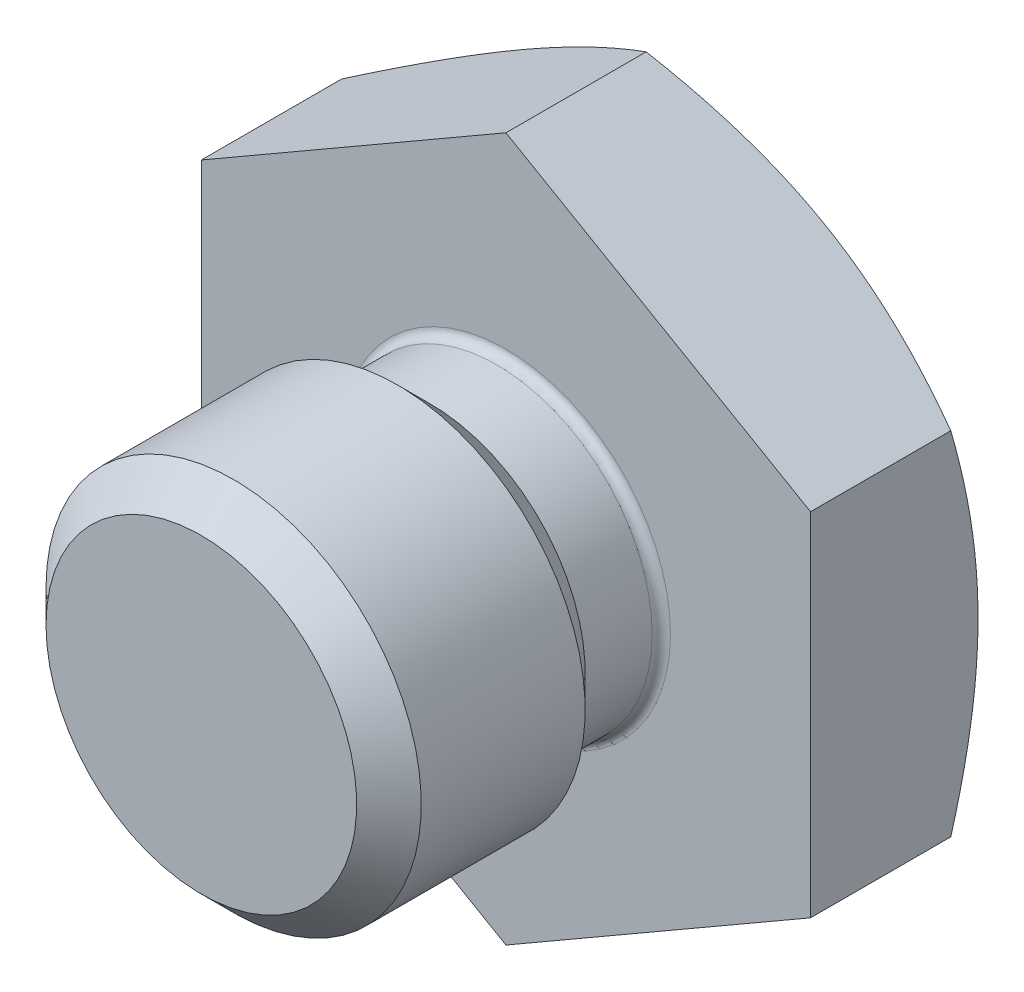
SolidWorks part; units mm, degrees
material "Alloy Steel"
ref_plane "Front Plane" through (0, 0, 0) normal (0, 0, 1) x (1, 0, 0)
ref_plane "Top Plane" through (0, 0, 0) normal (0, 1, 0) x (1, 0, 0)
ref_plane "Right Plane" through (0, 0, 0) normal (1, 0, 0) x (0, 0, -1)
sketch "Sketch1" plane through (0, 0, 0) normal (1, 0, 0) x (0, 0, -1)
  line L0 (0, 0) -> (-83.4165, 0) construction
  line L1 (0, 24.7927) -> (0, 6.477)
  line L2 (0, 6.477) -> (-3.175, 6.477)
  line L3 (-3.175, 6.477) -> (-4.5212, 7.8232)
  line L4 (-4.5212, 7.8232) -> (-11.3538, 7.8232)
  line L5 (-11.3538, 7.8232) -> (-12.7, 6.477)
  line L6 (-12.7, 6.477) -> (-12.7, 0)
  line L7 (-12.7, 0) -> (14.2748, 0)
  line L8 (0, 24.7927) -> (14.2408, 0.127)
  arc A0 (14.2748, 0) -> (14.2408, 0.127) centre (14.0208, 0) ccw
  dimension "D1" = 14.2748
  dimension "D7" = 0.254
  dimension "D2" = 15.6464
  dimension "D3" = 45
  dimension "D4" = 12.954
  dimension "D5" = 3.175
  dimension "D6" = 60
  dimension "D8" = 12.7
revolve "Revolve1" add sketch "Sketch1" angle 360 about L0
sketch "Sketch2" plane through (0, 0, 0) normal (0, 0, 1) x (1, 0, 0)
  line L1 (0, 14.6647) -> (-12.7, 7.3323)
  line L2 (-12.7, 7.3323) -> (-12.7, -7.3323)
  line L3 (-12.7, -7.3323) -> (0, -14.6647)
  line L4 (0, -14.6647) -> (12.7, -7.3323)
  line L5 (12.7, -7.3323) -> (12.7, 7.3323)
  line L6 (12.7, 7.3323) -> (0, 14.6647)
  circle A0 centre (0, 0) radius 12.7 construction
  dimension "D1" = 25.4
extrude "Cut-Extrude1" cut sketch "Sketch2" against normal through all flip side to cut
fillet "Fillet1" radius 0.381 1 edges at (-6.477, 0, 0)
